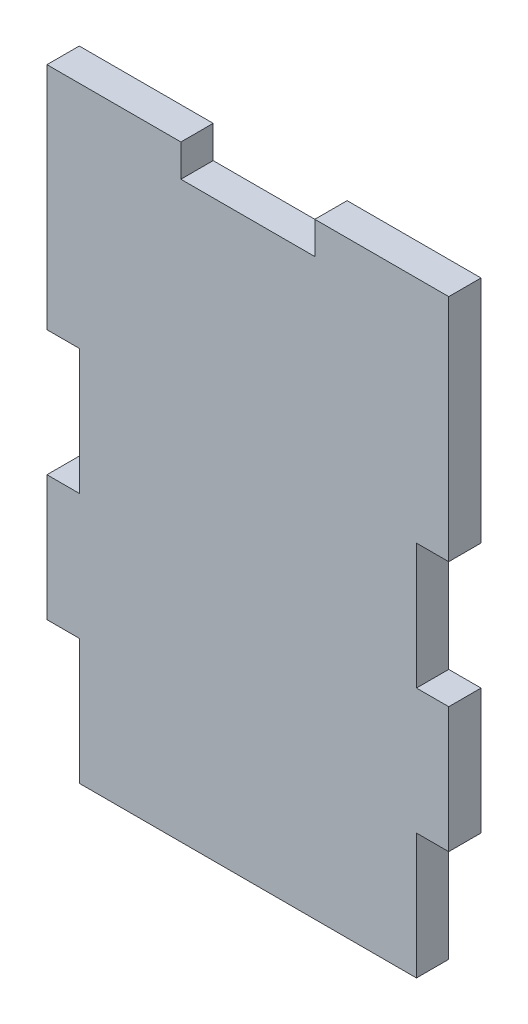
SolidWorks part; units mm, degrees
ref_plane "Front Plane" through (0, 0, 0) normal (0, 0, 1) x (1, 0, 0)
ref_plane "Top Plane" through (0, 0, 0) normal (0, 1, 0) x (1, 0, 0)
ref_plane "Right Plane" through (0, 0, 0) normal (1, 0, 0) x (0, 0, -1)
sketch "Sketch1" plane through (0, 0, 0) normal (0, 0, 1) x (1, 0, 0)
  line L0 (25.75, 26.25) -> (25.75, 17.5) construction
  line L1 (0, 0) -> (23.5, 0)
  line L2 (0, 0) -> (0, 40)
  line L3 (0, 40) -> (23.5, 40)
  line L4 (23.5, 0) -> (23.5, 40)
  line L9 (23.5, 40) -> (25.75, 40)
  line L10 (23.5, 40) -> (23.5, 26.25)
  line L11 (23.5, 26.25) -> (25.75, 26.25)
  line L12 (25.75, 40) -> (25.75, 26.25)
  line L13 (11.75, 0) -> (11.75, 40) construction
  line L14 (16.4167, 42.25) -> (7.0833, 42.25) construction
  line L35 (-2.25, 40) -> (7.0833, 40)
  line L36 (-2.25, 40) -> (-2.25, 42.25)
  line L37 (-2.25, 42.25) -> (7.0833, 42.25)
  line L38 (7.0833, 40) -> (7.0833, 42.25)
  line L39 (25.75, 40) -> (16.4167, 40)
  line L40 (25.75, 40) -> (25.75, 42.25)
  line L41 (25.75, 42.25) -> (16.4167, 42.25)
  line L42 (16.4167, 40) -> (16.4167, 42.25)
  line L43 (11.75, 40) -> (11.75, 42.25) construction
  line L44 (25.75, 8.75) -> (25.75, 0) construction
  line L45 (25.75, 17.5) -> (23.5, 17.5)
  line L46 (25.75, 17.5) -> (25.75, 8.75)
  line L47 (25.75, 8.75) -> (23.5, 8.75)
  line L48 (23.5, 17.5) -> (23.5, 8.75)
  line L49 (-2.25, 8.75) -> (0, 8.75)
  line L54 (0, 17.5) -> (0, 8.75)
  line L55 (-2.25, 17.5) -> (0, 17.5)
  line L56 (-2.25, 17.5) -> (-2.25, 8.75)
  line L57 (0, 26.25) -> (-2.25, 26.25)
  line L58 (-2.25, 40) -> (-2.25, 26.25)
  line L59 (0, 40) -> (-2.25, 40)
  line L60 (0, 40) -> (0, 26.25)
  dimension "D1" = 2.25
  dimension "D2" = 23.5
  dimension "D3" = 40
  dimension "D4" = 8.75
extrude "Boss-Extrude1" add sketch "Sketch1" along normal blind 2.25
equation "\"veneer_thickness\"= 0.5mm"
equation "\"thick\"= 1.75mm"
equation "\"D1@Boss-Extrude1\"=\"thick\" + \"veneer_thickness\""
equation "\"D2@Sketch1\"=20.000mm+\"thick\"*2"
equation "\"D1@Sketch1\"=\"thick\"+\"veneer_thickness\""
